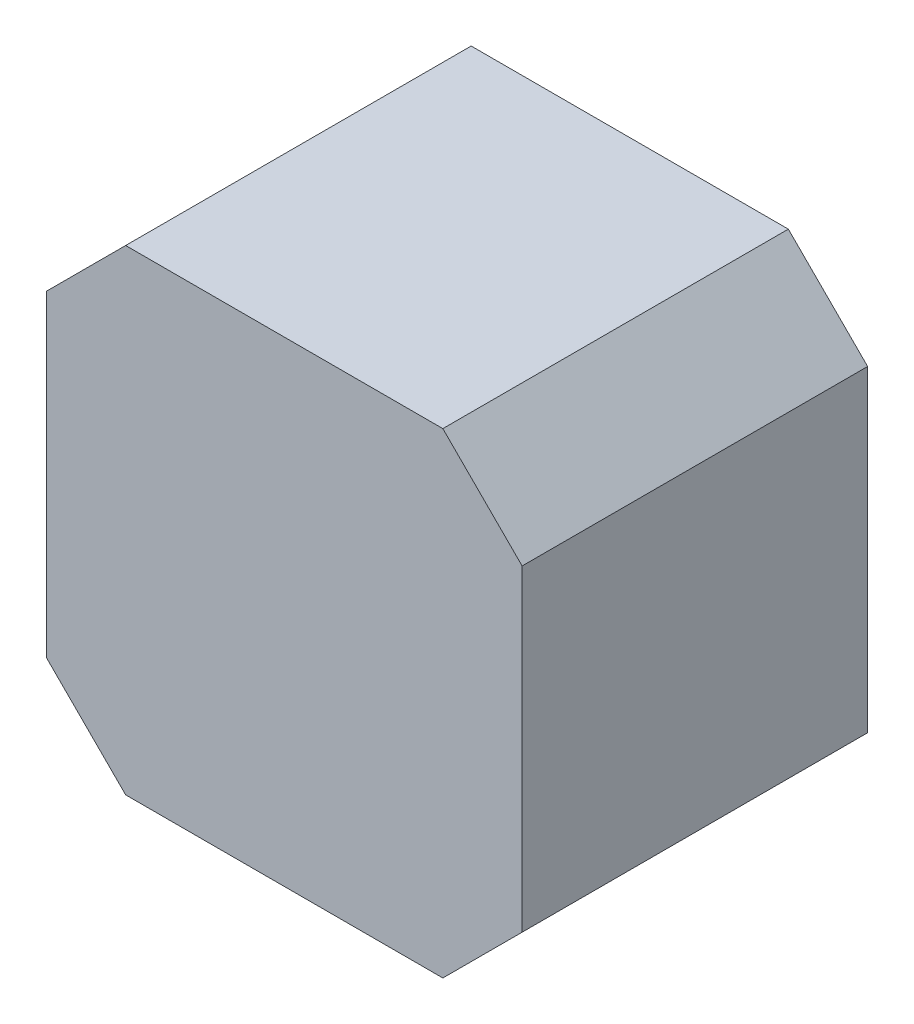
SolidWorks part; units mm, degrees
material "Acero aleado"
ref_plane "Alzado" through (0, 0, 0) normal (0, 0, 1) x (1, 0, 0)
ref_plane "Planta" through (0, 0, 0) normal (0, 1, 0) x (1, 0, 0)
ref_plane "Vista lateral" through (0, 0, 0) normal (1, 0, 0) x (0, 0, -1)
sketch "Croquis1" plane through (0, 0, 0) normal (0, 0, 1) x (1, 0, 0)
  line L0 (-14, 21) -> (-21, 14)
  line L1 (-14, 21) -> (14, 21)
  line L2 (-21, 14) -> (-21, -14)
  line L3 (-14, -21) -> (14, -21)
  line L4 (21, 14) -> (21, -14)
  line L5 (-21, 21) -> (21, -21) construction
  line L6 (-21, -21) -> (21, 21) construction
  line L7 (14, 21) -> (21, 14)
  line L8 (21, -14) -> (14, -21)
  line L9 (-21, -14) -> (-14, -21)
  point P0 (0, 0)
  dimension "D1" = 42
  dimension "D2" = 42
extrude "Saliente-Extruir1" add sketch "Croquis1" along normal blind 30.5
